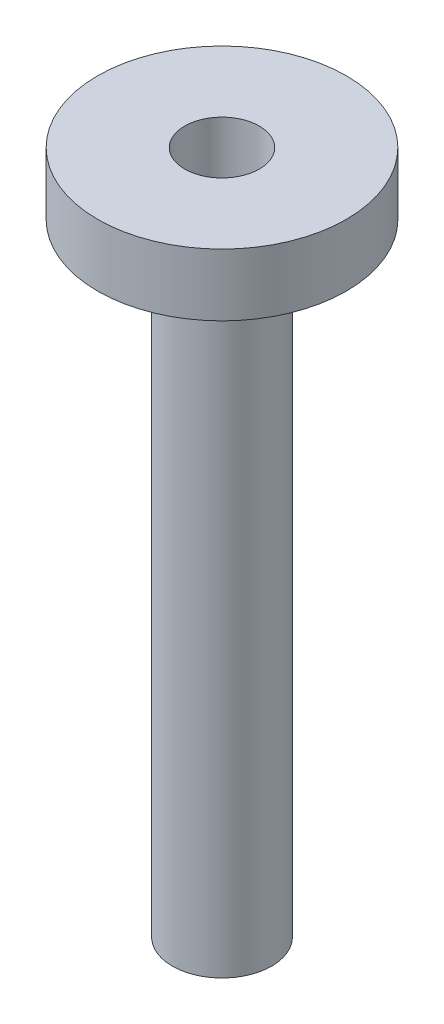
SolidWorks part; units mm, degrees
ref_plane "Front Plane" through (0, 0, 0) normal (0, 0, 1) x (1, 0, 0)
ref_plane "Top Plane" through (0, 0, 0) normal (0, 1, 0) x (1, 0, 0)
ref_plane "Right Plane" through (0, 0, 0) normal (1, 0, 0) x (0, 0, -1)
sketch "Sketch1" plane through (0, 0, 0) normal (0, 0, 1) x (1, 0, 0)
  line L0 (-3.81, 0) -> (-12.7, 0)
  line L1 (-12.7, 0) -> (-12.7, -6.35)
  line L2 (-12.7, -6.35) -> (-11.1125, -6.35)
  line L3 (-11.1125, -6.35) -> (-11.1125, -4.318)
  line L4 (-11.1125, -4.318) -> (-8.0645, -4.318)
  line L5 (-8.0645, -4.318) -> (-8.0645, -6.35)
  line L6 (-8.0645, -6.35) -> (-5.08, -6.35)
  line L7 (-5.08, -6.35) -> (-5.08, -69.85)
  line L8 (-5.08, -69.85) -> (-3.81, -68.58)
  line L9 (-3.81, -68.58) -> (-3.81, 0)
  line L10 (0, 0) -> (0, -4.7723) construction
  dimension "D1" = 1.5875
  dimension "D2" = 2.032
  dimension "D3" = 3.048
  dimension "D4" = 12.7
  dimension "D5" = 3.81
  dimension "D6" = 5.08
  dimension "D7" = 45
  dimension "D8" = 63.5
  dimension "D9" = 6.35
revolve "Revolve1" add sketch "Sketch1" angle 360 about L10
